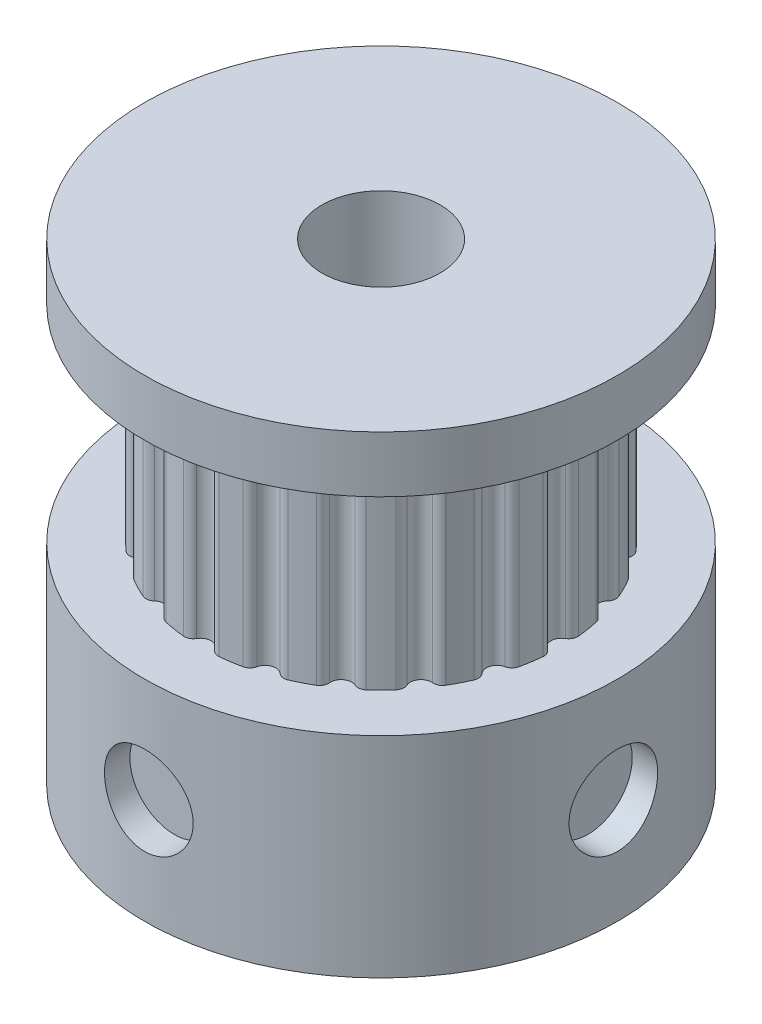
SolidWorks part; units mm, degrees
ref_plane "Front Plane" through (0, 0, 0) normal (0, 0, 1) x (1, 0, 0)
ref_plane "Top Plane" through (0, 0, 0) normal (0, 1, 0) x (1, 0, 0)
ref_plane "Right Plane" through (0, 0, 0) normal (1, 0, 0) x (0, 0, -1)
sketch "Sketch2" plane through (0, 0, 0) normal (0, 0, 1) x (1, 0, 0)
  line L1 (2, 8.9) -> (8, 8.9)
  line L2 (8, 8.9) -> (8, 7)
  line L3 (8, 7) -> (6.11, 7)
  line L4 (6.11, 7) -> (6.11, 0)
  line L5 (6.11, 0) -> (8, 0)
  line L6 (8, 0) -> (8, -7.1)
  line L7 (8, -7.1) -> (2, -7.1)
  line L8 (0, -8) -> (0, 8) construction
  line L9 (2, 8.9) -> (2, -7.1)
  point P13 (0, 0)
  dimension "D1" = 7
  dimension "D2" = 7.1
  dimension "D3" = 16
  dimension "D4" = 8
  dimension "D5" = 6.11
  dimension "D6" = 16
  dimension "D7" = 2
revolve "Revolve1" add sketch "Sketch2" angle 360 about L8
sketch "Sketch3" plane through (0, 7, 0) normal (0, -1, 0) x (1, 0, 0)
  line L0 (0, 0) -> (0, 6.11) construction
  line L1 (0, 5.75) -> (0.3118, 5.93) construction
  line L2 (0, 5.75) -> (0.7984, 5.75) construction
  line L3 (0, 5.75) -> (-0.3118, 5.93) construction
  circle A0 centre (0, 0) radius 6.11 construction
  circle A1 centre (0, 0) radius 6.11
  circle A2 centre (0, 0) radius 5.75
  arc A3 (0.3598, 6.0994) -> (-0.3598, 6.0994) centre (0, 6.11) ccw construction
  arc A4 (0.6042, 6.0801) -> (0.3118, 5.93) centre (0.5742, 5.7785) ccw
  arc A5 (-0.3118, 5.93) -> (-0.6042, 6.0801) centre (-0.5742, 5.7785) ccw
  arc A6 (-0.3118, 5.93) -> (0.3118, 5.93) centre (0, 6.11) ccw
  arc A7 (1.536, 5.7361) -> (1.3042, 5.9692) centre (1.2395, 5.6731) ccw
  arc A8 (1.536, 5.7361) -> (2.129, 5.5434) centre (1.8881, 5.811) ccw
  arc A9 (2.4535, 5.5958) -> (2.129, 5.5434) centre (2.3318, 5.3182) ccw
  arc A10 (3.2333, 4.9807) -> (3.0849, 5.274) centre (2.9319, 5.0124) ccw
  arc A11 (3.2333, 4.9807) -> (3.7378, 4.6142) centre (3.5914, 4.9431) ccw
  arc A12 (4.0626, 4.5637) -> (3.7378, 4.6142) centre (3.8611, 4.3373) ccw
  arc A13 (4.6142, 3.7378) -> (4.5637, 4.0626) centre (4.3373, 3.8611) ccw
  arc A14 (4.6142, 3.7378) -> (4.9807, 3.2333) centre (4.9431, 3.5914) ccw
  arc A15 (5.274, 3.0849) -> (4.9807, 3.2333) centre (5.0124, 2.9319) ccw
  arc A16 (5.5434, 2.129) -> (5.5958, 2.4535) centre (5.3182, 2.3318) ccw
  arc A17 (5.5434, 2.129) -> (5.7361, 1.536) centre (5.811, 1.8881) ccw
  arc A18 (5.9692, 1.3042) -> (5.7361, 1.536) centre (5.6731, 1.2395) ccw
  arc A19 (5.93, 0.3118) -> (6.0801, 0.6042) centre (5.7785, 0.5742) ccw
  arc A20 (5.93, 0.3118) -> (5.93, -0.3118) centre (6.11, 0) ccw
  arc A21 (6.0801, -0.6042) -> (5.93, -0.3118) centre (5.7785, -0.5742) ccw
  arc A22 (5.7361, -1.536) -> (5.9692, -1.3042) centre (5.6731, -1.2395) ccw
  arc A23 (5.7361, -1.536) -> (5.5434, -2.129) centre (5.811, -1.8881) ccw
  arc A24 (5.5958, -2.4535) -> (5.5434, -2.129) centre (5.3182, -2.3318) ccw
  arc A25 (4.9807, -3.2333) -> (5.274, -3.0849) centre (5.0124, -2.9319) ccw
  arc A26 (4.9807, -3.2333) -> (4.6142, -3.7378) centre (4.9431, -3.5914) ccw
  arc A27 (4.5637, -4.0626) -> (4.6142, -3.7378) centre (4.3373, -3.8611) ccw
  arc A28 (3.7378, -4.6142) -> (4.0626, -4.5637) centre (3.8611, -4.3373) ccw
  arc A29 (3.7378, -4.6142) -> (3.2333, -4.9807) centre (3.5914, -4.9431) ccw
  arc A30 (3.0849, -5.274) -> (3.2333, -4.9807) centre (2.9319, -5.0124) ccw
  arc A31 (2.129, -5.5434) -> (2.4535, -5.5958) centre (2.3318, -5.3182) ccw
  arc A32 (2.129, -5.5434) -> (1.536, -5.7361) centre (1.8881, -5.811) ccw
  arc A33 (1.3042, -5.9692) -> (1.536, -5.7361) centre (1.2395, -5.6731) ccw
  arc A34 (0.3118, -5.93) -> (0.6042, -6.0801) centre (0.5742, -5.7785) ccw
  arc A35 (0.3118, -5.93) -> (-0.3118, -5.93) centre (0, -6.11) ccw
  arc A36 (-0.6042, -6.0801) -> (-0.3118, -5.93) centre (-0.5742, -5.7785) ccw
  arc A37 (-1.536, -5.7361) -> (-1.3042, -5.9692) centre (-1.2395, -5.6731) ccw
  arc A38 (-1.536, -5.7361) -> (-2.129, -5.5434) centre (-1.8881, -5.811) ccw
  arc A39 (-2.4535, -5.5958) -> (-2.129, -5.5434) centre (-2.3318, -5.3182) ccw
  arc A40 (-3.2333, -4.9807) -> (-3.0849, -5.274) centre (-2.9319, -5.0124) ccw
  arc A41 (-3.2333, -4.9807) -> (-3.7378, -4.6142) centre (-3.5914, -4.9431) ccw
  arc A42 (-4.0626, -4.5637) -> (-3.7378, -4.6142) centre (-3.8611, -4.3373) ccw
  arc A43 (-4.6142, -3.7378) -> (-4.5637, -4.0626) centre (-4.3373, -3.8611) ccw
  arc A44 (-4.6142, -3.7378) -> (-4.9807, -3.2333) centre (-4.9431, -3.5914) ccw
  arc A45 (-5.274, -3.0849) -> (-4.9807, -3.2333) centre (-5.0124, -2.9319) ccw
  arc A46 (-5.5434, -2.129) -> (-5.5958, -2.4535) centre (-5.3182, -2.3318) ccw
  arc A47 (-5.5434, -2.129) -> (-5.7361, -1.536) centre (-5.811, -1.8881) ccw
  arc A48 (-5.9692, -1.3042) -> (-5.7361, -1.536) centre (-5.6731, -1.2395) ccw
  arc A49 (-5.93, -0.3118) -> (-6.0801, -0.6042) centre (-5.7785, -0.5742) ccw
  arc A50 (-5.93, -0.3118) -> (-5.93, 0.3118) centre (-6.11, 0) ccw
  arc A51 (-6.0801, 0.6042) -> (-5.93, 0.3118) centre (-5.7785, 0.5742) ccw
  arc A52 (-5.7361, 1.536) -> (-5.9692, 1.3042) centre (-5.6731, 1.2395) ccw
  arc A53 (-5.7361, 1.536) -> (-5.5434, 2.129) centre (-5.811, 1.8881) ccw
  arc A54 (-5.5958, 2.4535) -> (-5.5434, 2.129) centre (-5.3182, 2.3318) ccw
  arc A55 (-4.9807, 3.2333) -> (-5.274, 3.0849) centre (-5.0124, 2.9319) ccw
  arc A56 (-4.9807, 3.2333) -> (-4.6142, 3.7378) centre (-4.9431, 3.5914) ccw
  arc A57 (-4.5637, 4.0626) -> (-4.6142, 3.7378) centre (-4.3373, 3.8611) ccw
  arc A58 (-3.7378, 4.6142) -> (-4.0626, 4.5637) centre (-3.8611, 4.3373) ccw
  arc A59 (-3.7378, 4.6142) -> (-3.2333, 4.9807) centre (-3.5914, 4.9431) ccw
  arc A60 (-3.0849, 5.274) -> (-3.2333, 4.9807) centre (-2.9319, 5.0124) ccw
  arc A61 (-2.129, 5.5434) -> (-2.4535, 5.5958) centre (-2.3318, 5.3182) ccw
  arc A62 (-2.129, 5.5434) -> (-1.536, 5.7361) centre (-1.8881, 5.811) ccw
  arc A63 (-1.3042, 5.9692) -> (-1.536, 5.7361) centre (-1.2395, 5.6731) ccw
  point P4 (0, 5.75)
  point P16 (-0.6042, 6.0801)
  point P18 (0.6042, 6.0801)
  point P154 (0, 0)
  dimension "D1" = 11.5
  dimension "D2" = 30
  dimension "D3" = 30
  dimension "D4" = 20
extrude "Cut-Extrude1" cut sketch "Sketch3" along normal up to surface (7 mm away) contours A6 A4 A1 A5 | A9 A1 A7 A8 | A12 A1 A10 A11 | A15 A1 A13 A14 | A18 A1 A16 A17 | A21 A1 A19 A20 | A24 A1 A22 A23 | A27 A1 A25 A26 | A30 A1 A28 A29 | A33 A1 A31 A32 | A36 A1 A34 A35 | A39 A1 A37 A38 | A42 A1 A40 A41 | A45 A1 A43 A44 | A48 A1 A46 A47 | A51 A1 A49 A50 | A54 A1 A52 A53 | A60 A1 A58 A59 | A63 A1 A61 A62 | A57 A1 A55 A56 up to face at (0, 0, -6.11)
ref_plane "Plane1" through (-8, 0, 0) normal (-1, 0, 0) x (0, 0, 1)
sketch "Sketch4" plane through (-8, 0, 0) normal (-1, 0, 0) x (0, 0, 1)
  line L0 (0, 0) -> (0, -7.1) construction
  line L1 (-8, -7.1) -> (8, -7.1) construction
  circle A0 centre (0, -3.55) radius 1.5
  dimension "D1" = 3
extrude "Cut-Extrude2" cut sketch "Sketch4" against normal blind 1
pattern_circular "CirPattern1" count 4 over 360 about axis through (0, 0, 0) along (0, 1, 0) of "Cut-Extrude2"
